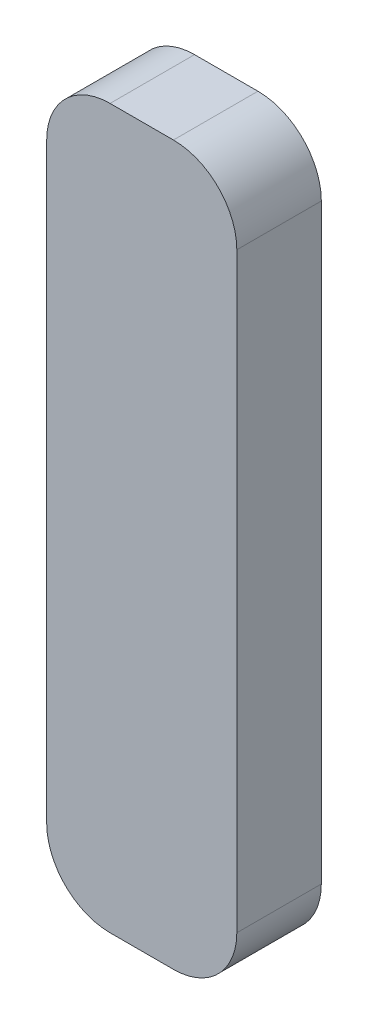
SolidWorks part; units mm, degrees
ref_plane "Plan de face" through (0, 0, 0) normal (0, 0, 1) x (1, 0, 0)
ref_plane "Plan de dessus" through (0, 0, 0) normal (0, 1, 0) x (1, 0, 0)
ref_plane "Plan de droite" through (0, 0, 0) normal (1, 0, 0) x (0, 0, -1)
sketch "Esquisse1" plane through (0, 0, 0) normal (0, 0, 1) x (1, 0, 0)
  line L1 (-27.0656, -46.2165) -> (-18.0656, -46.2165)
  line L2 (-27.0656, -46.2165) -> (-27.0656, -80.2165)
  line L3 (-27.0656, -80.2165) -> (-18.0656, -80.2165)
  line L4 (-18.0656, -46.2165) -> (-18.0656, -80.2165)
extrude "Boss.-Extru.1" add sketch "Esquisse1" along normal blind 4
fillet "Congé1" radius 3 4 edges at (-27.0656, -80.2165, 2) (-18.0656, -80.2165, 2) (-27.0656, -46.2165, 2) (-18.0656, -46.2165, 2)
